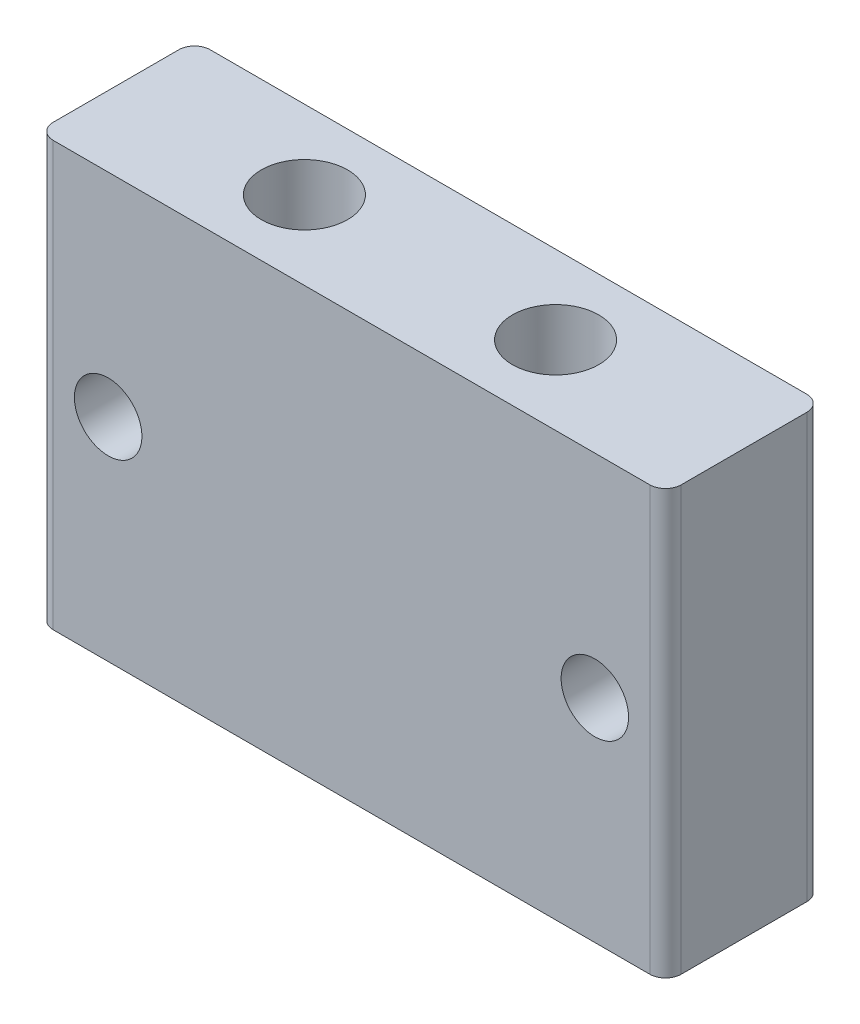
SolidWorks part; units mm, degrees
ref_plane "Front Plane" through (0, 0, 0) normal (0, 0, 1) x (1, 0, 0)
ref_plane "Top Plane" through (0, 0, 0) normal (0, 1, 0) x (1, 0, 0)
ref_plane "Right Plane" through (0, 0, 0) normal (1, 0, 0) x (0, 0, -1)
sketch "Sketch1" plane through (0, 0, 0) normal (0, 1, 0) x (1, 0, 0)
  line L1 (0, 0) -> (40, 0)
  line L2 (0, 0) -> (0, 10)
  line L3 (0, 10) -> (40, 10)
  line L4 (40, 0) -> (40, 10)
  dimension "D1" = 10
  dimension "D2" = 40
extrude "Boss-Extrude1" add sketch "Sketch1" along normal blind 27
sketch "Sketch4" plane through (0, 0, -10) normal (0, 0, -1) x (-1, 0, 0)
  line L0 (-20, 27) -> (-20, 0) construction
  line L1 (-40, 27) -> (0, 27) construction
  line L2 (-40, 0) -> (0, 0) construction
  line L3 (-35.5, 13.5) -> (-4.5, 13.5) construction
  circle A0 centre (-35.5, 13.5) radius 2.15
  circle A1 centre (-4.5, 13.5) radius 2.15
  point P10 (0, 0)
  dimension "D2" = 4.3
  dimension "D1" = 31
  dimension "D3" = 13.5
extrude "Cut-Extrude1" cut sketch "Sketch4" against normal through all and the other way through all
fillet "Fillet1" radius 1 4 edges at (0, 13.5, -10) (0, 13.5, 0) (40, 13.5, -10) (40, 13.5, 0)
sketch "Sketch5" plane through (0, 27, 0) normal (0, 1, 0) x (1, 0, 0)
  line L0 (12, 5) -> (28, 5) construction
  line L1 (39, 10) -> (1, 10) construction
  line L2 (1, 0) -> (39, 0) construction
  line L3 (20, 10) -> (20, 0) construction
  circle A0 centre (12, 5) radius 2.75
  circle A1 centre (28, 5) radius 2.75
  point P10 (0, 0)
  dimension "D1" = 5.5
  dimension "D2" = 16
extrude "Cut-Extrude2" cut sketch "Sketch5" against normal through all and the other way through all
